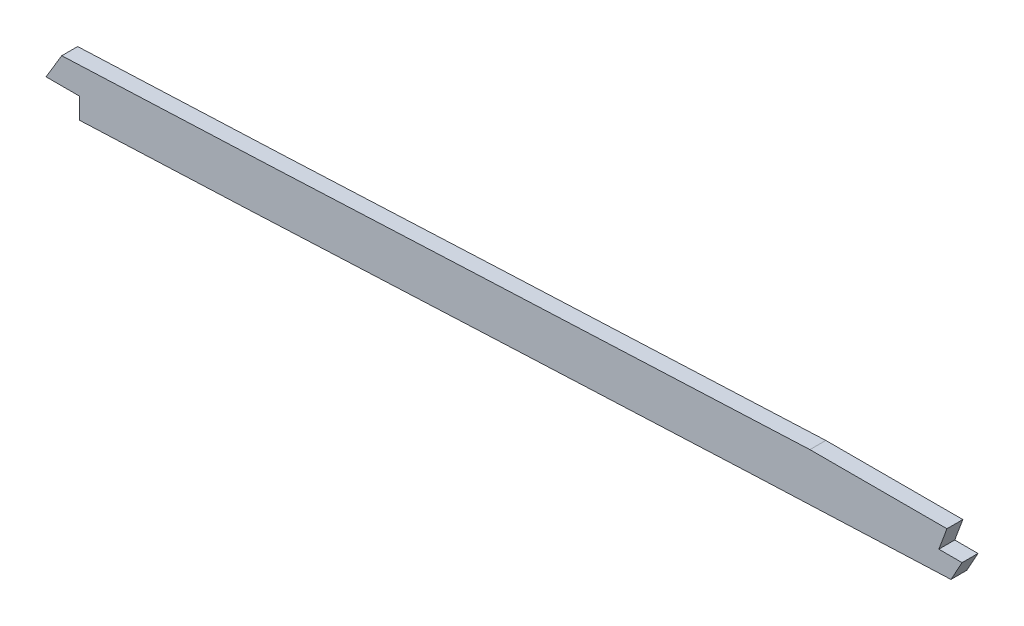
SolidWorks part; units mm, degrees
ref_plane "Front Plane" through (0, 0, 0) normal (0, 0, 1) x (1, 0, 0)
ref_plane "Top Plane" through (0, 0, 0) normal (0, 1, 0) x (1, 0, 0)
ref_plane "Right Plane" through (0, 0, 0) normal (1, 0, 0) x (0, 0, -1)
sketch "Sketch1" plane through (0, 0, 0) normal (0, 0, 1) x (1, 0, 0)
  line L0 (1046.2855, 53.4707) -> (499.61, 53.4707) construction
  line L1 (55, 0) -> (-55, 0) construction
  line L2 (1046.2855, -53.4707) -> (499.61, -53.4707)
  line L3 (1046.2855, -34.4207) -> (499.61, -34.4207)
  line L4 (99.06, -18.1493) -> (99.06, -37.7415)
  line L5 (2669.54, 9.5231) -> (2669.54, -9.569)
  spline S0 degree 5 poles (2699.7923, 7.5245) (2639.6368, 11.6572) (2579.4813, 15.4358) (2518.4981, 19.1485) (2436.3555, 23.2524) (2354.213, 26.6315) (2332.5703, 27.481) (2156.2686, 34.3778) (1979.9669, 41.6286) (1824.1143, 52.7713) (1636.9286, 53.5796) (1449.7429, 53.454) (1418.0067, 53.4707) (1324.8993, 53.4707) (1231.7919, 53.4707) (1170.4413, 53.4707) (1108.7841, 53.4707) (1047.1269, 53.4707) (1046.8464, 53.4707) (1046.5659, 53.4707) (1046.2855, 53.4707) knots 100.654805 100.654805 100.654805 100.654805 100.654805 100.654805 130.927897 130.927897 130.927897 141.337055 141.337055 141.337055 218.101815 218.101815 218.101815 233.772059 233.772059 233.772059 264.077723 264.077723 264.077723 264.216209 264.216209 264.216209 264.216209 264.216209 264.216209 weights 1 1 1 1 1 1 1 1 1 1 1 1 1 1 1 1 1 1 1 1 1 construction
  spline S1 degree 5 poles (499.61, 53.4707) (492.1368, 53.4707) (484.7543, 53.4707) (477.443, 53.4707) (448.5166, 53.4707) (419.5901, 53.4707) (398.3681, 53.4707) (355.6475, 53.4707) (312.927, 53.4707) (289.2351, 53.4703) (265.365, 53.4707) (241.4948, 53.4707) (241.4716, 53.4707) (241.4484, 53.4707) (241.4251, 53.4707) knots 19.90683 19.90683 19.90683 19.90683 19.90683 19.90683 23.637897 23.637897 23.637897 34.276546 34.276546 34.276546 46.401341 46.401341 46.401341 46.413154 46.413154 46.413154 46.413154 46.413154 46.413154 weights 1 1 1 1 1 1 1 1 1 1 1 1 1 1 1 construction
  spline S2 degree 5 poles (241.4251, 53.4707) (224.2869, 53.4707) (207.1495, 53.4673) (190.2039, 52.6866) (151.6561, 49.0319) (113.1083, 41.5037) (91.9499, 36.3426) (71.313, 30.9696) (50.6762, 24.7565) knots 0 0 0 0 0 0 8.713816 8.713816 8.713816 19.90683 19.90683 19.90683 19.90683 19.90683 19.90683 weights 1 1 1 1 1 1 1 1 1 construction
  spline S3 degree 5 poles (241.4251, -53.4707) (224.2869, -53.4707) (207.1495, -53.4673) (190.2039, -52.6866) (151.6561, -49.0319) (113.1083, -41.5037) (91.9499, -36.3426) (71.313, -30.9696) (50.6762, -24.7565) knots 0 0 0 0 0 0 8.713816 8.713816 8.713816 19.90683 19.90683 19.90683 19.90683 19.90683 19.90683 weights 1 1 1 1 1 1 1 1 1
  spline S4 degree 5 poles (499.61, -53.4707) (492.1368, -53.4707) (484.7543, -53.4707) (477.443, -53.4707) (448.5166, -53.4707) (419.5901, -53.4707) (398.3681, -53.4707) (355.6475, -53.4707) (312.927, -53.4707) (289.2351, -53.4703) (265.365, -53.4707) (241.4948, -53.4707) (241.4716, -53.4707) (241.4484, -53.4707) (241.4251, -53.4707) knots 19.90683 19.90683 19.90683 19.90683 19.90683 19.90683 23.637897 23.637897 23.637897 34.276546 34.276546 34.276546 46.401341 46.401341 46.401341 46.413154 46.413154 46.413154 46.413154 46.413154 46.413154 weights 1 1 1 1 1 1 1 1 1 1 1 1 1 1 1
  spline S5 degree 5 poles (2699.7923, -7.5245) (2639.6368, -11.6572) (2579.4813, -15.4358) (2518.4981, -19.1485) (2436.3555, -23.2524) (2354.213, -26.6315) (2332.5703, -27.481) (2156.2686, -34.3778) (1979.9669, -41.6286) (1824.1143, -52.7713) (1636.9286, -53.5796) (1449.7429, -53.454) (1418.0067, -53.4707) (1324.8993, -53.4707) (1231.7919, -53.4707) (1170.4413, -53.4707) (1108.7841, -53.4707) (1047.1269, -53.4707) (1046.8464, -53.4707) (1046.5659, -53.4707) (1046.2855, -53.4707) knots 100.654805 100.654805 100.654805 100.654805 100.654805 100.654805 130.927897 130.927897 130.927897 141.337055 141.337055 141.337055 218.101815 218.101815 218.101815 233.772059 233.772059 233.772059 264.077723 264.077723 264.077723 264.216209 264.216209 264.216209 264.216209 264.216209 264.216209 weights 1 1 1 1 1 1 1 1 1 1 1 1 1 1 1 1 1 1 1 1 1
  spline S6 degree 1 poles (2698.4867, 11.4807) (1046.2855, -34.4207) knots 0 0 1 1 construction
  spline S7 degree 1 poles (499.61, -34.4207) (241.4252, -34.4207) knots 0 0 1 1 construction
  spline S8 degree 1 poles (241.4252, -34.4207) (56.168, -6.5153) knots 0 0 1 1 construction
  spline S9 degree 3 poles (2698.4867, 11.4807) (2691.2474, 10.9833) (2679.1952, 10.1655) (2662.2765, 9.0388) (2635.6663, 7.2925) (2596.8577, 4.8261) (2545.7297, 1.7583) (2494.4053, -1.0986) (2451.533, -3.2666) (2417.1983, -4.8671) (2391.4571, -6.0036) (2365.6347, -7.0869) (2339.5463, -8.1377) (2313.4661, -9.1651) (2287.6124, -10.1795) (2261.7633, -11.201) (2227.2853, -12.5838) (2184.1756, -14.3661) (2132.4291, -16.6074) (2063.4255, -19.7089) (1977.1749, -23.7005) (1873.7325, -28.1494) (1770.3746, -31.6575) (1667.0857, -33.7931) (1581.0111, -34.3832) (1512.074, -34.4278) (1443.0615, -34.4095) (1356.8009, -34.4244) (1218.7946, -34.4185) (1115.289, -34.4207) (1046.2855, -34.4207) knots 100.654805 100.654805 100.654805 100.654805 102.842388 104.300777 105.766098 110.877392 115.988686 121.09998 126.211274 128.766921 131.322568 133.878215 136.433862 138.989509 141.545156 144.100803 146.656449 151.767743 156.879037 161.990331 172.212919 182.435507 192.658094 202.880682 213.10327 218.214564 223.325858 233.548445 243.771033 264.216209 264.216209 264.216209 264.216209
  spline S10 degree 3 poles (499.61, -34.4207) (488.6147, -34.4207) (472.2364, -34.4207) (449.9402, -34.4207) (427.7713, -34.4207) (405.8747, -34.4207) (384.5849, -34.4207) (368.9002, -34.4207) (353.3766, -34.4207) (332.6085, -34.4207) (306.2878, -34.4206) (274.0235, -34.4205) (252.271, -34.4207) (241.4252, -34.4207) knots 19.90683 19.90683 19.90683 19.90683 23.22012 24.876765 26.533411 29.846701 31.503346 33.159992 34.816637 36.473282 39.786573 43.099863 46.413154 46.413154 46.413154 46.413154
  spline S11 degree 3 poles (241.4252, -34.4207) (239.3949, -34.4207) (235.3223, -34.4205) (227.2744, -34.3987) (217.3194, -34.2975) (205.5307, -33.9764) (189.9633, -33.2126) (170.697, -31.5435) (147.5333, -28.3144) (125.4828, -24.2021) (107.4399, -20.1965) (92.2061, -16.4882) (75.9505, -12.2555) (63.6202, -8.7589) (56.168, -6.5153) knots 0 0 0 0 0.622088 1.244177 2.488354 3.732531 4.976707 7.465061 9.953415 12.441768 14.558235 15.802412 17.418476 19.90683 19.90683 19.90683 19.90683
  point P2 (0, 0)
  dimension "D1" = 50.6762
  dimension "D3" = 99.06
  dimension "D4" = 2669.54
  dimension "D2" = 19.05
extrude "Boss-Extrude1" add sketch "Sketch1" along normal mid plane 6.35 contours S10 S11 L4 S3 S4 L2 S5 L5 S9 L3
sketch "Sketch2" plane through (0, 0, 3.175) normal (0, 0, 1) x (1, 0, 0)
  line L0 (2187.01, -14.2633) -> (2312.9875, -14.2633)
  line L1 (2312.9875, -14.2633) -> (2312.9875, -9.1833)
  spline S0 degree 3 poles (689.0175, 232.3189) (4033.8285, 148.9311) (3356.6623, 54.6077) (2635.6663, 7.2925) (2596.8577, 4.8261) (2545.7297, 1.7583) (2494.4053, -1.0986) (2451.533, -3.2666) (2417.1983, -4.8671) (2391.4571, -6.0036) (2365.6347, -7.0869) (2339.5463, -8.1377) (2313.4661, -9.1651) (2287.6124, -10.1795) (2261.7633, -11.201) (2227.2853, -12.5838) (2184.1756, -14.3661) (2132.4291, -16.6074) (2063.4255, -19.7089) (1977.1749, -23.7005) (1873.7325, -28.1494) (1770.3746, -31.6575) (1667.0857, -33.7931) (1581.0111, -34.3832) (1512.074, -34.4278) (1443.0615, -34.4095) (1356.8009, -34.4244) (551.9641, -34.3896) (-218.4198, -34.7282) (-953.6342, -29.9632) knots -106.828462 -106.828462 -106.828462 -106.828462 104.300777 105.766098 110.877392 115.988686 121.09998 126.211274 128.766921 131.322568 133.878215 136.433862 138.989509 141.545156 144.100803 146.656449 151.767743 156.879037 161.990331 172.212919 182.435507 192.658094 202.880682 213.10327 218.214564 223.325858 233.548445 243.771033 461.793666 461.793666 461.793666 461.793666 only from (2669.54, 9.5231) to (1046.2855, -34.4207) construction
  spline S1 degree 3 poles (2669.54, 9.5231) (2667.1265, 9.3624) (2659.8616, 8.8803) (2635.6663, 7.2925) (2596.8577, 4.8261) (2545.7297, 1.7583) (2494.4053, -1.0986) (2451.533, -3.2666) (2417.1983, -4.8671) (2391.4571, -6.0036) (2365.6347, -7.0869) (2339.5463, -8.1377) (2313.4661, -9.1651) (2287.6124, -10.1795) (2261.7633, -11.201) (2227.2853, -12.5838) (2184.1756, -14.3661) (2132.4291, -16.6074) (2063.4255, -19.7089) (1977.1749, -23.7005) (1873.7325, -28.1494) (1770.3746, -31.6575) (1667.0857, -33.7931) (1581.0111, -34.3832) (1512.074, -34.4278) (1443.0615, -34.4095) (1356.8009, -34.4244) (1218.7946, -34.4185) (1115.289, -34.4207) (1046.2855, -34.4207) knots 103.571583 103.571583 103.571583 103.571583 104.300777 105.766098 110.877392 115.988686 121.09998 126.211274 128.766921 131.322568 133.878215 136.433862 138.989509 141.545156 144.100803 146.656449 151.767743 156.879037 161.990331 172.212919 182.435507 192.658094 202.880682 213.10327 218.214564 223.325858 233.548445 243.771033 264.216209 264.216209 264.216209 264.216209
  point P2 (0, 0)
  spline M9 degree 3 poles (2698.4867, 11.4807) (2691.2474, 10.9833) (2679.1952, 10.1655) (2662.2765, 9.0388) (2635.6663, 7.2925) (2596.8577, 4.8261) (2545.7297, 1.7583) (2494.4053, -1.0986) (2451.533, -3.2666) (2417.1983, -4.8671) (2391.4571, -6.0036) (2365.6347, -7.0869) (2339.5463, -8.1377) (2313.4661, -9.1651) (2287.6124, -10.1795) (2261.7633, -11.201) (2227.2853, -12.5838) (2184.1756, -14.3661) (2132.4291, -16.6074) (2063.4255, -19.7089) (1977.1749, -23.7005) (1873.7325, -28.1494) (1770.3746, -31.6575) (1667.0857, -33.7931) (1581.0111, -34.3832) (1512.074, -34.4278) (1443.0615, -34.4095) (1356.8009, -34.4244) (1218.7946, -34.4185) (1115.289, -34.4207) (1046.2855, -34.4207) knots 100.654805 100.654805 100.654805 100.654805 102.842388 104.300777 105.766098 110.877392 115.988686 121.09998 126.211274 128.766921 131.322568 133.878215 136.433862 138.989509 141.545156 144.100803 146.656449 151.767743 156.879037 161.990331 172.212919 182.435507 192.658094 202.880682 213.10327 218.214564 223.325858 233.548445 243.771033 264.216209 264.216209 264.216209 264.216209 only from (2669.54, 9.5231) to (1046.2855, -34.4207)
  dimension "D1" = 2312.9875
  dimension "D2" = 5.08
extrude "Cut-Extrude1" cut sketch "Sketch2" against normal through all contours L0 L1 M9
fillet "Fillet1" radius 2.54 6 edges at (2669.54, -9.569, 0) (2669.54, 9.5231, 0) (99.06, -37.7415, 0) (99.06, -18.1493, 0) (2312.9875, -14.2633, 0)
sketch "Sketch3" plane through (0, 0, 3.175) normal (0, 0, 1) x (1, 0, 0)
  line L9 (2187.01, -14.2633) -> (2310.4475, -14.2633) construction
  line L22 (1888.275, -27.4246) -> (1881.9861, -37.8581)
  line L23 (1881.9861, -37.8581) -> (1895.4063, -37.8581)
  line L24 (1895.4063, -37.8581) -> (1895.4063, -46.2049)
  line L25 (2241.7242, -14.2633) -> (2238.4954, -22.96)
  line L26 (2238.4954, -22.96) -> (2247.7774, -22.96)
  line L27 (2247.7774, -22.96) -> (2243.3377, -31.0069)
  line L28 (1888.275, -27.4246) -> (1888.275, -1.8072)
  line L29 (1888.275, -1.8072) -> (-121.1913, 139.5963)
  line L30 (-121.1913, 139.5963) -> (-62.2557, -449.7599)
  line L31 (-62.2557, -449.7599) -> (1895.4063, -50.2169)
  line L32 (1895.4063, -50.2169) -> (1895.4063, -46.2049)
  line L33 (2241.7242, -14.2633) -> (2241.7242, 2.0499)
  line L34 (2241.7242, 2.0499) -> (2717.8549, 35.479)
  line L35 (2717.8549, 35.479) -> (2717.8549, -90.6402)
  line L36 (2717.8549, -90.6402) -> (2243.3377, -37.8581)
  line L37 (2243.3377, -37.8581) -> (2243.3377, -31.0069)
  spline S2 degree 3 poles (2187.01, -14.2633) (2186.0643, -14.3032) (2167.8725, -15.0722) (2132.4291, -16.6074) (2063.4255, -19.7089) (1977.1749, -23.7005) (1873.7325, -28.1494) (1770.3746, -31.6575) (1667.0857, -33.7931) (1581.0111, -34.3832) (1512.074, -34.4278) (1443.0615, -34.4095) (1356.8009, -34.4244) (1218.7946, -34.4185) (1115.289, -34.4207) (1046.2855, -34.4207) knots 151.487489 151.487489 151.487489 151.487489 151.767743 156.879037 161.990331 172.212919 182.435507 192.658094 202.880682 213.10327 218.214564 223.325858 233.548445 243.771033 264.216209 264.216209 264.216209 264.216209 construction
  spline S3 degree 5 poles (2667.1682, -9.7266) (2613.4902, -13.2886) (2559.6385, -16.6207) (2505.242, -19.8061) (2429.7275, -23.525) (2354.213, -26.6315) (2332.5703, -27.481) (2156.2686, -34.3778) (1979.9669, -41.6286) (1824.1143, -52.7713) (1636.9286, -53.5796) (1449.7429, -53.454) (1418.0067, -53.4707) (1324.8993, -53.4707) (1231.7919, -53.4707) (1170.4413, -53.4707) (1108.7841, -53.4707) (1047.1269, -53.4707) (1046.8464, -53.4707) (1046.5659, -53.4707) (1046.2855, -53.4707) knots 103.937447 103.937447 103.937447 103.937447 103.937447 103.937447 130.927897 130.927897 130.927897 141.337055 141.337055 141.337055 218.101815 218.101815 218.101815 233.772059 233.772059 233.772059 264.077723 264.077723 264.077723 264.216209 264.216209 264.216209 264.216209 264.216209 264.216209 weights 1 1 1 1 1 1 1 1 1 1 1 1 1 1 1 1 1 1 1 1 1 construction
extrude "Cut-Extrude2" cut sketch "Sketch3" against normal blind 7.62
